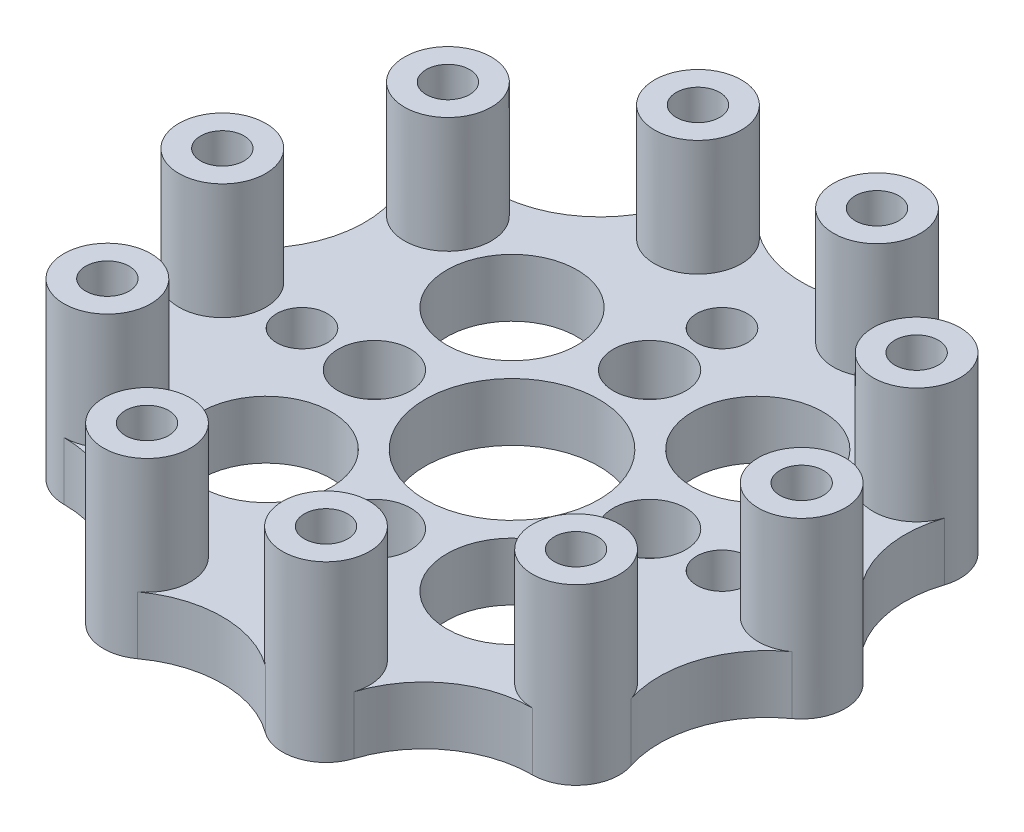
SolidWorks part; units mm, degrees
ref_plane "前视基准面" through (0, 0, 0) normal (0, 0, 1) x (1, 0, 0)
ref_plane "上视基准面" through (0, 0, 0) normal (0, 1, 0) x (1, 0, 0)
ref_plane "右视基准面" through (0, 0, 0) normal (1, 0, 0) x (0, 0, -1)
sketch "草图1" plane through (0, 0, 0) normal (0, 1, 0) x (1, 0, 0)
  line L0 (9.5, 0) -> (0, 0) construction
  line L1 (0, 0) -> (8.4853, 8.4853) construction
  circle A0 centre (0, 0) radius 20 construction
  arc A1 (21.7541, -2.4337) -> (21.7541, 2.4337) centre (20, 0) ccw
  arc A2 (16.1689, -14.7557) -> (19.03, -10.8178) centre (16.1803, -11.7557) ccw
  arc A3 (4.4078, -21.4414) -> (9.037, -19.9373) centre (6.1803, -19.0211) ccw
  arc A4 (-9.037, -19.9373) -> (-4.4078, -21.4414) centre (-6.1803, -19.0211) ccw
  arc A5 (-19.03, -10.8178) -> (-16.1689, -14.7557) centre (-16.1803, -11.7557) ccw
  arc A6 (-21.7541, 2.4337) -> (-21.7541, -2.4337) centre (-20, 0) ccw
  arc A7 (-16.1689, 14.7557) -> (-19.03, 10.8178) centre (-16.1803, 11.7557) ccw
  arc A8 (-4.4078, 21.4414) -> (-9.037, 19.9373) centre (-6.1803, 19.0211) ccw
  arc A9 (9.037, 19.9373) -> (4.4078, 21.4414) centre (6.1803, 19.0211) ccw
  arc A10 (19.03, 10.8178) -> (16.1689, 14.7557) centre (16.1803, 11.7557) ccw
  arc A11 (19.03, 10.8178) -> (21.7541, 2.4337) centre (26.1159, 8.4856) ccw
  arc A12 (21.7541, -2.4337) -> (19.03, -10.8178) centre (26.1159, -8.4856) ccw
  arc A13 (16.1689, -14.7557) -> (9.037, -19.9373) centre (16.1405, -22.2155) ccw
  arc A14 (4.4078, -21.4414) -> (-4.4078, -21.4414) centre (0, -27.4599) ccw
  arc A15 (-9.037, -19.9373) -> (-16.1689, -14.7557) centre (-16.1405, -22.2155) ccw
  arc A16 (-19.03, -10.8178) -> (-21.7541, -2.4337) centre (-26.1159, -8.4856) ccw
  arc A17 (-21.7541, 2.4337) -> (-19.03, 10.8178) centre (-26.1159, 8.4856) ccw
  arc A18 (-16.1689, 14.7557) -> (-9.037, 19.9373) centre (-16.1405, 22.2155) ccw
  arc A19 (-4.4078, 21.4414) -> (4.4078, 21.4414) centre (0, 27.4599) ccw
  arc A20 (9.037, 19.9373) -> (16.1689, 14.7557) centre (16.1405, 22.2155) ccw
  circle A21 centre (20, 0) radius 1.5
  circle A22 centre (16.1803, -11.7557) radius 1.5
  circle A23 centre (6.1803, -19.0211) radius 1.5
  circle A24 centre (-6.1803, -19.0211) radius 1.5
  circle A25 centre (-16.1803, -11.7557) radius 1.5
  circle A26 centre (-20, 0) radius 1.5
  circle A27 centre (-16.1803, 11.7557) radius 1.5
  circle A28 centre (-6.1803, 19.0211) radius 1.5
  circle A29 centre (6.1803, 19.0211) radius 1.5
  circle A30 centre (16.1803, 11.7557) radius 1.5
  circle A31 centre (9.5, 0) radius 1.5
  circle A32 centre (0, -9.5) radius 1.5
  circle A33 centre (-9.5, 0) radius 1.5
  circle A34 centre (0, 9.5) radius 1.5
  circle A35 centre (0, 0) radius 6
  circle A36 centre (8.4853, 8.4853) radius 4.5
  circle A37 centre (8.4853, -8.4853) radius 4.5
  circle A38 centre (-8.4853, -8.4853) radius 4.5
  circle A39 centre (-8.4853, 8.4853) radius 4.5
  circle A40 centre (14.5, 0) radius 1.75
  circle A41 centre (20, 0) radius 3 construction
  circle A42 centre (0, -14.5) radius 1.75
  circle A43 centre (-14.5, 0) radius 1.75
  circle A44 centre (0, 14.5) radius 1.75
  point P26 (0, 0)
  point P57 (0, 0)
  point P67 (0, 0)
  point P76 (0, 0)
  point P84 (0, 0)
  point P94 (0, 0)
  dimension "D1" = 40
  dimension "D2" = 6
  dimension "D5" = 3
  dimension "D8" = 3
  dimension "D10" = 12
  dimension "D12" = 9
  dimension "D16" = 3.5
  dimension "D7" = 9.5
  dimension "D11" = 45
  dimension "D13" = 12
  dimension "D15" = 14.5
  dimension "D3" = 10
  dimension "D4" = 10
  dimension "D6" = 10
  dimension "D9" = 4
  dimension "D14" = 4
  dimension "D17" = 4
extrude "凸台-拉伸1" add sketch "草图1" along normal blind 4
sketch "草图2" plane through (0, 4, 0) normal (0, 1, 0) x (1, 0, 0)
  circle A0 centre (9.5, 0) radius 2.5
  circle A1 centre (0, -9.5) radius 2.5
  circle A2 centre (-9.5, 0) radius 2.5
  circle A3 centre (0, 9.5) radius 2.5
  point P12 (0, 0)
  dimension "D1" = 5
  dimension "D2" = 4
extrude "切除-拉伸1" cut sketch "草图2" against normal blind 3.5
sketch "草图3" plane through (0, 4, 0) normal (0, 1, 0) x (1, 0, 0)
  circle A0 centre (20, 0) radius 3
  arc A1 (21.7541, -2.4337) -> (21.7541, 2.4337) centre (20, 0) ccw construction
  circle A2 centre (20, 0) radius 1.5 construction
  circle A3 centre (20, 0) radius 1.5
  circle A4 centre (16.1803, -11.7557) radius 3
  circle A5 centre (16.1803, -11.7557) radius 1.5
  circle A6 centre (6.1803, -19.0211) radius 3
  circle A7 centre (6.1803, -19.0211) radius 1.5
  circle A8 centre (-6.1803, -19.0211) radius 3
  circle A9 centre (-6.1803, -19.0211) radius 1.5
  circle A10 centre (-16.1803, -11.7557) radius 3
  circle A11 centre (-16.1803, -11.7557) radius 1.5
  circle A12 centre (-20, 0) radius 3
  circle A13 centre (-20, 0) radius 1.5
  circle A14 centre (-16.1803, 11.7557) radius 3
  circle A15 centre (-16.1803, 11.7557) radius 1.5
  circle A16 centre (-6.1803, 19.0211) radius 3
  circle A17 centre (-6.1803, 19.0211) radius 1.5
  circle A18 centre (6.1803, 19.0211) radius 3
  circle A19 centre (6.1803, 19.0211) radius 1.5
  circle A20 centre (16.1803, 11.7557) radius 3
  circle A21 centre (16.1803, 11.7557) radius 1.5
  point P38 (0, 0)
  dimension "D1" = 10
extrude "凸台-拉伸2" add sketch "草图3" along normal blind 8
sketch "草图4" plane through (0, 0, 0) normal (0, -1, 0) x (1, 0, 0)
  circle A0 centre (20, 0) radius 2.4995
  circle A1 centre (16.1803, -11.7557) radius 2.4995
  circle A2 centre (6.1803, -19.0211) radius 2.4995
  circle A3 centre (-6.1803, -19.0211) radius 2.4995
  circle A4 centre (-16.1803, -11.7557) radius 2.4995
  circle A5 centre (-20, 0) radius 2.4995
  circle A6 centre (-16.1803, 11.7557) radius 2.4995
  circle A7 centre (-6.1803, 19.0211) radius 2.4995
  circle A8 centre (6.1803, 19.0211) radius 2.4995
  circle A9 centre (16.1803, 11.7557) radius 2.4995
  point P24 (0, 0)
  dimension "D1" = 4.999
  dimension "D2" = 10
extrude "切除-拉伸2" cut sketch "草图4" against normal blind 4
